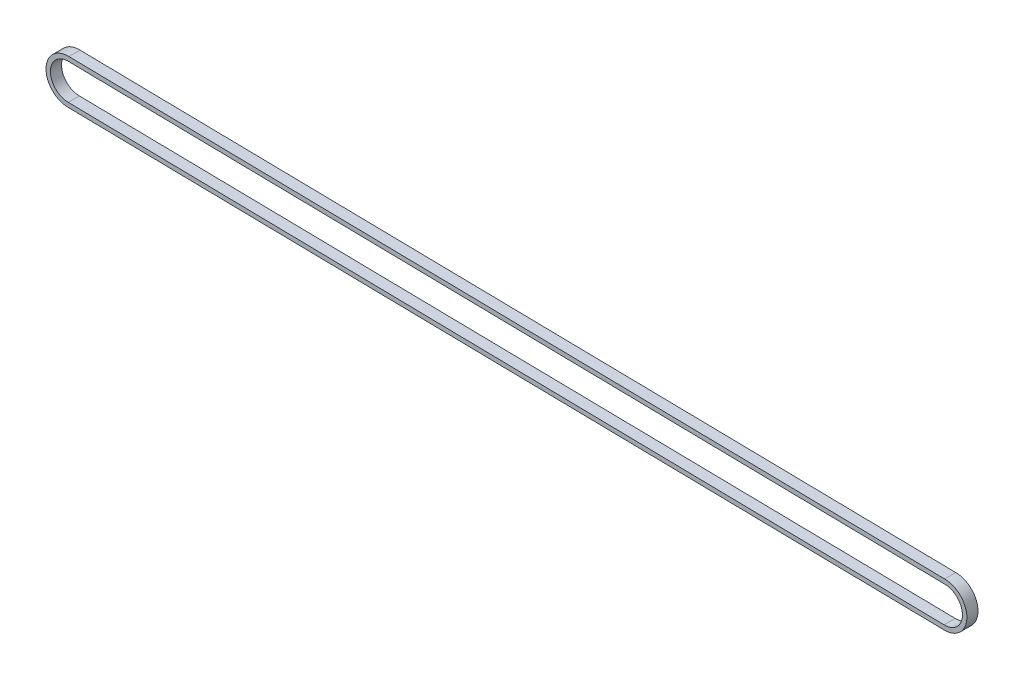
SolidWorks part; units mm, degrees
ref_plane "Front Plane" through (0, 0, 0) normal (0, 0, 1) x (1, 0, 0)
ref_plane "Top Plane" through (0, 0, 0) normal (0, 1, 0) x (1, 0, 0)
ref_plane "Right Plane" through (0, 0, 0) normal (1, 0, 0) x (0, 0, -1)
sketch "Sketch3" plane through (0, 0, 0) normal (0, 0, 1) x (1, 0, 0)
  line L0 (-32.2949, 8.1977) -> (361.7974, 1.6332)
  line L1 (-32.6279, -11.7967) -> (361.4644, -18.3612)
  line L2 (-32.6279, -9.7967) -> (361.531, -16.3624)
  line L3 (361.7974, -0.3668) -> (-32.3615, 6.1988)
  arc A1 (-32.2949, 8.1977) -> (-32.6279, -11.7967) centre (-32.6279, -1.7967) ccw
  arc A2 (361.4644, -18.3612) -> (361.7974, 1.6332) centre (361.7974, -8.3668) ccw
  arc A3 (-32.3615, 6.1988) -> (-32.6279, -9.7967) centre (-32.6279, -1.7967) ccw
  arc A4 (361.531, -16.3624) -> (361.7974, -0.3668) centre (361.7974, -8.3668) ccw
extrude "Boss-Extrude3" add sketch "Sketch3" along normal blind 5
